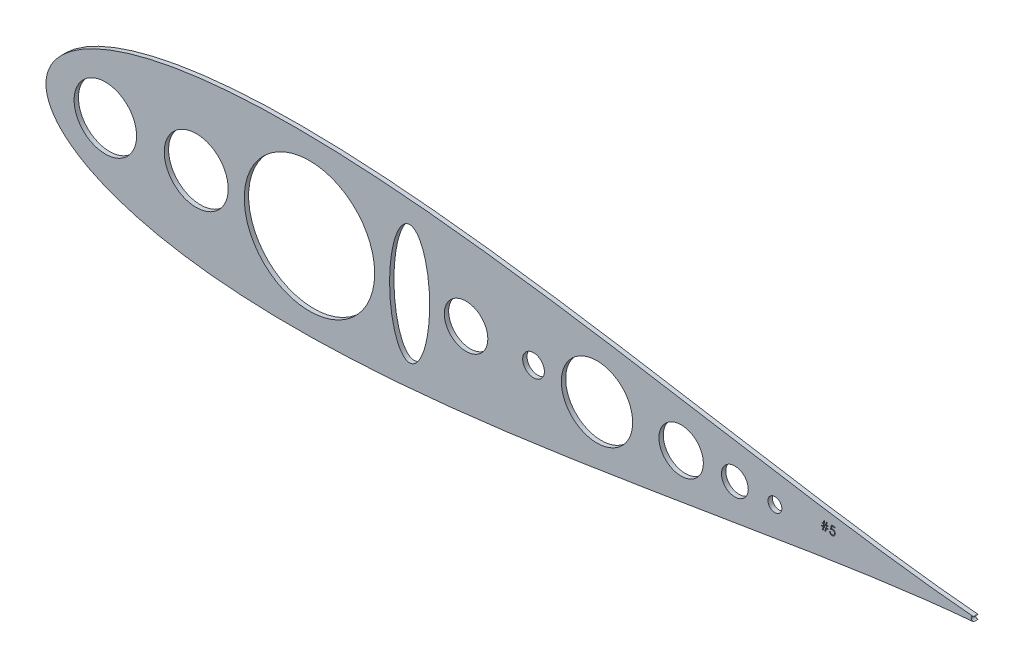
SolidWorks part; units mm, degrees
ref_plane "Front Plane" through (0, 0, 0) normal (0, 0, 1) x (1, 0, 0)
ref_plane "Top Plane" through (0, 0, 0) normal (0, 1, 0) x (1, 0, 0)
ref_plane "Right Plane" through (0, 0, 0) normal (1, 0, 0) x (0, 0, -1)
sketch "Model" plane through (0, 0, 0) normal (0, 0, 1) x (1, 0, 0)
  line L0 (738.2935, 524.3398) -> (738.2935, 524.0142)
  line L1 (738.2935, 524.0142) -> (737.3226, 524.0142)
  line L2 (737.3226, 524.0142) -> (737.0591, 522.2557)
  line L3 (737.0591, 522.2557) -> (736.6653, 522.2557)
  line L4 (736.6653, 522.2557) -> (736.9288, 524.0142)
  line L5 (736.9288, 524.0142) -> (735.8898, 524.0142)
  line L6 (735.8898, 524.0142) -> (735.6263, 522.2557)
  line L7 (735.6263, 522.2557) -> (735.2324, 522.2557)
  line L8 (735.2324, 522.2557) -> (735.496, 524.0142)
  line L9 (735.496, 524.0142) -> (734.6463, 524.0142)
  line L10 (734.6463, 524.0142) -> (734.6463, 524.3398)
  line L11 (734.6463, 524.3398) -> (735.5449, 524.3398)
  line L12 (735.5449, 524.3398) -> (735.7209, 525.5121)
  line L13 (735.7209, 525.5121) -> (734.7765, 525.5121)
  line L14 (734.7765, 525.5121) -> (734.7765, 525.8378)
  line L15 (734.7765, 525.8378) -> (735.7697, 525.8378)
  line L16 (735.7697, 525.8378) -> (736.014, 527.466)
  line L17 (736.014, 527.466) -> (736.4068, 527.466)
  line L18 (736.4068, 527.466) -> (736.1626, 525.8378)
  line L19 (736.1626, 525.8378) -> (737.2026, 525.8378)
  line L20 (737.2026, 525.8378) -> (737.4468, 527.466)
  line L21 (737.4468, 527.466) -> (737.8396, 527.466)
  line L22 (737.8396, 527.466) -> (737.5954, 525.8378)
  line L23 (737.5954, 525.8378) -> (738.4237, 525.8378)
  line L24 (738.4237, 525.8378) -> (738.4237, 525.5121)
  line L25 (738.4237, 525.5121) -> (737.5465, 525.5121)
  line L26 (737.5465, 525.5121) -> (737.3715, 524.3398)
  line L27 (737.3715, 524.3398) -> (738.2935, 524.3398)
  line L28 (737.1537, 525.5121) -> (736.1137, 525.5121)
  line L29 (736.1137, 525.5121) -> (735.9387, 524.3398)
  line L30 (735.9387, 524.3398) -> (736.9777, 524.3398)
  line L31 (736.9777, 524.3398) -> (737.1537, 525.5121)
  line L32 (742.4617, 527.3357) -> (742.4617, 526.8147)
  line L33 (742.4617, 526.8147) -> (740.7337, 526.8147)
  line L34 (740.7337, 526.8147) -> (740.46, 525.4786)
  line L35 (740.46, 525.4786) -> (740.6218, 525.5213)
  line L36 (740.6218, 525.5213) -> (740.7755, 525.5528)
  line L37 (740.7755, 525.5528) -> (740.921, 525.5712)
  line L38 (740.921, 525.5712) -> (741.0584, 525.5773)
  line L39 (741.0584, 525.5773) -> (741.2283, 525.5701)
  line L40 (741.2283, 525.5701) -> (741.3911, 525.5478)
  line L41 (741.3911, 525.5478) -> (741.5458, 525.5111)
  line L42 (741.5458, 525.5111) -> (741.6934, 525.4602)
  line L43 (741.6934, 525.4602) -> (741.8328, 525.3951)
  line L44 (741.8328, 525.3951) -> (741.9641, 525.3147)
  line L45 (741.9641, 525.3147) -> (742.0882, 525.2201)
  line L46 (742.0882, 525.2201) -> (742.2052, 525.1102)
  line L47 (742.2052, 525.1102) -> (742.3111, 524.9891)
  line L48 (742.3111, 524.9891) -> (742.4026, 524.8609)
  line L49 (742.4026, 524.8609) -> (742.481, 524.7235)
  line L50 (742.481, 524.7235) -> (742.5441, 524.579)
  line L51 (742.5441, 524.579) -> (742.594, 524.4253)
  line L52 (742.594, 524.4253) -> (742.6286, 524.2635)
  line L53 (742.6286, 524.2635) -> (742.6499, 524.0936)
  line L54 (742.6499, 524.0936) -> (742.6571, 523.9155)
  line L55 (742.6571, 523.9155) -> (742.653, 523.7913)
  line L56 (742.653, 523.7913) -> (742.6428, 523.6692)
  line L57 (742.6428, 523.6692) -> (742.6245, 523.5502)
  line L58 (742.6245, 523.5502) -> (742.5991, 523.4331)
  line L59 (742.5991, 523.4331) -> (742.5665, 523.3192)
  line L60 (742.5665, 523.3192) -> (742.5268, 523.2082)
  line L61 (742.5268, 523.2082) -> (742.479, 523.0993)
  line L62 (742.479, 523.0993) -> (742.425, 522.9925)
  line L63 (742.425, 522.9925) -> (742.365, 522.8907)
  line L64 (742.365, 522.8907) -> (742.2989, 522.7951)
  line L65 (742.2989, 522.7951) -> (742.2286, 522.7055)
  line L66 (742.2286, 522.7055) -> (742.1533, 522.6221)
  line L67 (742.1533, 522.6221) -> (742.0719, 522.5447)
  line L68 (742.0719, 522.5447) -> (741.9854, 522.4735)
  line L69 (741.9854, 522.4735) -> (741.8949, 522.4084)
  line L70 (741.8949, 522.4084) -> (741.7982, 522.3494)
  line L71 (741.7982, 522.3494) -> (741.6974, 522.2964)
  line L72 (741.6974, 522.2964) -> (741.5926, 522.2517)
  line L73 (741.5926, 522.2517) -> (741.4847, 522.213)
  line L74 (741.4847, 522.213) -> (741.3728, 522.1814)
  line L75 (741.3728, 522.1814) -> (741.2568, 522.157)
  line L76 (741.2568, 522.157) -> (741.1367, 522.1397)
  line L77 (741.1367, 522.1397) -> (741.0126, 522.1285)
  line L78 (741.0126, 522.1285) -> (740.8854, 522.1255)
  line L79 (740.8854, 522.1255) -> (740.7337, 522.1316)
  line L80 (740.7337, 522.1316) -> (740.5882, 522.1509)
  line L81 (740.5882, 522.1509) -> (740.4488, 522.1814)
  line L82 (740.4488, 522.1814) -> (740.3155, 522.2252)
  line L83 (740.3155, 522.2252) -> (740.1883, 522.2812)
  line L84 (740.1883, 522.2812) -> (740.0672, 522.3504)
  line L85 (740.0672, 522.3504) -> (739.9512, 522.4308)
  line L86 (739.9512, 522.4308) -> (739.8423, 522.5244)
  line L87 (739.8423, 522.5244) -> (739.7416, 522.6282)
  line L88 (739.7416, 522.6282) -> (739.652, 522.7391)
  line L89 (739.652, 522.7391) -> (739.5726, 522.8572)
  line L90 (739.5726, 522.8572) -> (739.5034, 522.9833)
  line L91 (739.5034, 522.9833) -> (739.4454, 523.1156)
  line L92 (739.4454, 523.1156) -> (739.3986, 523.2561)
  line L93 (739.3986, 523.2561) -> (739.362, 523.4036)
  line L94 (739.362, 523.4036) -> (739.3355, 523.5583)
  line L95 (739.3355, 523.5583) -> (739.7914, 523.5583)
  line L96 (739.7914, 523.5583) -> (739.828, 523.4138)
  line L97 (739.828, 523.4138) -> (739.8749, 523.2846)
  line L98 (739.8749, 523.2846) -> (739.9329, 523.1685)
  line L99 (739.9329, 523.1685) -> (740.001, 523.0668)
  line L100 (740.001, 523.0668) -> (740.0814, 522.9772)
  line L101 (740.0814, 522.9772) -> (740.174, 522.8968)
  line L102 (740.174, 522.8968) -> (740.2789, 522.8246)
  line L103 (740.2789, 522.8246) -> (740.3959, 522.7625)
  line L104 (740.3959, 522.7625) -> (740.52, 522.7116)
  line L105 (740.52, 522.7116) -> (740.6483, 522.676)
  line L106 (740.6483, 522.676) -> (740.7785, 522.6536)
  line L107 (740.7785, 522.6536) -> (740.9118, 522.6465)
  line L108 (740.9118, 522.6465) -> (741.0421, 522.6526)
  line L109 (741.0421, 522.6526) -> (741.1672, 522.6699)
  line L110 (741.1672, 522.6699) -> (741.2883, 522.6984)
  line L111 (741.2883, 522.6984) -> (741.4044, 522.7391)
  line L112 (741.4044, 522.7391) -> (741.5153, 522.79)
  line L113 (741.5153, 522.79) -> (741.6221, 522.8541)
  line L114 (741.6221, 522.8541) -> (741.7239, 522.9284)
  line L115 (741.7239, 522.9284) -> (741.8216, 523.0149)
  line L116 (741.8216, 523.0149) -> (741.9101, 523.1095)
  line L117 (741.9101, 523.1095) -> (741.9875, 523.2103)
  line L118 (741.9875, 523.2103) -> (742.0526, 523.3171)
  line L119 (742.0526, 523.3171) -> (742.1065, 523.4291)
  line L120 (742.1065, 523.4291) -> (742.1482, 523.5471)
  line L121 (742.1482, 523.5471) -> (742.1778, 523.6702)
  line L122 (742.1778, 523.6702) -> (742.1951, 523.7995)
  line L123 (742.1951, 523.7995) -> (742.2012, 523.9348)
  line L124 (742.2012, 523.9348) -> (742.1961, 524.0569)
  line L125 (742.1961, 524.0569) -> (742.1808, 524.1729)
  line L126 (742.1808, 524.1729) -> (742.1543, 524.2828)
  line L127 (742.1543, 524.2828) -> (742.1177, 524.3866)
  line L128 (742.1177, 524.3866) -> (742.0709, 524.4854)
  line L129 (742.0709, 524.4854) -> (742.0139, 524.578)
  line L130 (742.0139, 524.578) -> (741.9457, 524.6645)
  line L131 (741.9457, 524.6645) -> (741.8674, 524.7449)
  line L132 (741.8674, 524.7449) -> (741.7809, 524.8181)
  line L133 (741.7809, 524.8181) -> (741.6862, 524.8812)
  line L134 (741.6862, 524.8812) -> (741.5855, 524.9341)
  line L135 (741.5855, 524.9341) -> (741.4776, 524.9789)
  line L136 (741.4776, 524.9789) -> (741.3626, 525.0125)
  line L137 (741.3626, 525.0125) -> (741.2405, 525.0369)
  line L138 (741.2405, 525.0369) -> (741.1123, 525.0512)
  line L139 (741.1123, 525.0512) -> (740.9759, 525.0562)
  line L140 (740.9759, 525.0562) -> (740.8579, 525.0522)
  line L141 (740.8579, 525.0522) -> (740.7327, 525.04)
  line L142 (740.7327, 525.04) -> (740.6025, 525.0196)
  line L143 (740.6025, 525.0196) -> (740.4651, 524.9911)
  line L144 (740.4651, 524.9911) -> (740.3226, 524.9545)
  line L145 (740.3226, 524.9545) -> (740.173, 524.9097)
  line L146 (740.173, 524.9097) -> (740.0183, 524.8568)
  line L147 (740.0183, 524.8568) -> (739.8565, 524.7957)
  line L148 (739.8565, 524.7957) -> (740.3776, 527.3357)
  line L149 (740.3776, 527.3357) -> (742.4617, 527.3357)
  circle A0 centre (316.6495, 521.1085) radius 18.2309
  circle A1 centre (707.4198, 521.1085) radius 4.0377
  circle A2 centre (684.0578, 521.1085) radius 7.8218
  circle A3 centre (652.7021, 521.1085) radius 12.9578
  circle A4 centre (603.5976, 521.1085) radius 20.8135
  circle A5 centre (566.5539, 521.1085) radius 6.35
  circle A6 centre (527.1839, 521.1085) radius 12.7
  circle A7 centre (435.7938, 521.1085) radius 38.053
  circle A8 centre (369.7039, 521.1085) radius 18.669
  arc A9 (823.4212, 522.34) -> (823.4192, 519.8762) centre (823.2427, 521.1082) ccw
  arc A10 (823.4212, 522.34) -> (823.0121, 522.4406) centre (822.9014, 521.1085) ccw
  arc A11 (823.0121, 519.7764) -> (823.4192, 519.8762) centre (822.9014, 521.1085) ccw
  ellipse E0 centre (494.2426, 521.1085) end of major axis (494.2426, 486.1605) minor radius 11.7082
  spline S0 degree 3 poles (823.0121, 522.4406) (822.5764, 522.4768) (819.2929, 522.7534) (812.8264, 523.3511) (803.2279, 524.3496) (792.5858, 525.5748) (780.94, 527.0342) (768.345, 528.7291) (754.8551, 530.6559) (740.5289, 532.8045) (725.4271, 535.1596) (709.6131, 537.7002) (693.1521, 540.4001) (676.1114, 543.2282) (658.5599, 546.1488) (640.5682, 549.1221) (622.2082, 552.1052) (603.5531, 555.0523) (584.6777, 557.9153) (565.658, 560.645) (546.5712, 563.1915) (527.4962, 565.5052) (508.5129, 567.5374) (489.7028, 569.2411) (471.1488, 570.572) (452.9349, 571.4888) (435.1468, 571.9548) (417.8712, 571.9375) (401.1964, 571.4095) (385.2119, 570.3502) (370.009, 568.7441) (355.6804, 566.584) (342.3218, 563.8693) (330.032, 560.6089) (318.9148, 556.8219) (309.0813, 552.5422) (300.6507, 547.8264) (293.7491, 542.7702) (288.4927, 537.5386) (284.934, 532.4085) (282.9495, 527.78) (282.1482, 524.0671) (281.9657, 521.1085) (282.1482, 518.1499) (282.9495, 514.437) (284.934, 509.8086) (288.4927, 504.6784) (293.7491, 499.4469) (300.6507, 494.3906) (309.0813, 489.6748) (318.9148, 485.3951) (330.032, 481.6082) (342.3218, 478.3478) (355.6804, 475.633) (370.009, 473.4729) (385.2119, 471.8669) (401.1964, 470.8075) (417.8712, 470.2795) (435.1468, 470.2622) (452.9349, 470.7282) (471.1488, 471.6451) (489.7028, 472.9759) (508.5129, 474.6796) (527.4962, 476.7118) (546.5712, 479.0255) (565.658, 481.572) (584.6777, 484.3017) (603.5531, 487.1647) (622.2082, 490.1118) (640.5682, 493.0949) (658.5599, 496.0683) (676.1114, 498.9888) (693.1521, 501.8169) (709.6131, 504.5168) (725.4271, 507.0575) (740.5289, 509.4126) (754.8551, 511.5611) (768.345, 513.4879) (780.94, 515.1828) (792.5858, 516.6422) (803.2279, 517.8674) (812.8264, 518.8659) (819.2929, 519.4636) (822.5764, 519.7402) (823.0121, 519.7764) knots 0.020157 0.020157 0.020157 0.020157 0.021271 0.028553 0.036781 0.04592 0.055932 0.066773 0.078397 0.090755 0.103793 0.117456 0.131686 0.146422 0.1616 0.177156 0.193024 0.209135 0.225421 0.241812 0.258238 0.274629 0.290914 0.307025 0.322893 0.338448 0.353626 0.368361 0.38259 0.396253 0.40929 0.421647 0.43327 0.444109 0.454119 0.463255 0.471479 0.478755 0.485052 0.490344 0.49461 0.497833 0.5 0.502167 0.50539 0.509656 0.514948 0.521245 0.528521 0.536745 0.545881 0.555891 0.56673 0.578353 0.59071 0.603747 0.61741 0.631639 0.646374 0.661552 0.677107 0.692975 0.709086 0.725371 0.741762 0.758188 0.774579 0.790865 0.806976 0.822844 0.8384 0.853578 0.868314 0.882544 0.896207 0.909245 0.921603 0.933227 0.944068 0.95408 0.963219 0.971447 0.978729 0.979843 0.979843 0.979843 0.979843
sketch "Sketch2" plane through (0, 0, 0) normal (0, 0, 1) x (1, 0, 0)
  line L0 (738.2935, 524.3398) -> (738.2935, 524.0142)
  line L1 (738.2935, 524.0142) -> (737.3226, 524.0142)
  line L2 (737.3226, 524.0142) -> (737.0591, 522.2557)
  line L3 (737.0591, 522.2557) -> (736.6653, 522.2557)
  line L4 (736.6653, 522.2557) -> (736.9288, 524.0142)
  line L5 (736.9288, 524.0142) -> (735.8898, 524.0142)
  line L6 (735.8898, 524.0142) -> (735.6263, 522.2557)
  line L7 (735.6263, 522.2557) -> (735.2324, 522.2557)
  line L8 (735.2324, 522.2557) -> (735.496, 524.0142)
  line L9 (735.496, 524.0142) -> (734.6463, 524.0142)
  line L10 (734.6463, 524.0142) -> (734.6463, 524.3398)
  line L11 (734.6463, 524.3398) -> (735.5449, 524.3398)
  line L12 (735.5449, 524.3398) -> (735.7209, 525.5121)
  line L13 (735.7209, 525.5121) -> (734.7765, 525.5121)
  line L14 (734.7765, 525.5121) -> (734.7765, 525.8378)
  line L15 (734.7765, 525.8378) -> (735.7697, 525.8378)
  line L16 (735.7697, 525.8378) -> (736.014, 527.466)
  line L17 (736.014, 527.466) -> (736.4068, 527.466)
  line L18 (736.4068, 527.466) -> (736.1626, 525.8378)
  line L19 (736.1626, 525.8378) -> (737.2026, 525.8378)
  line L20 (737.2026, 525.8378) -> (737.4468, 527.466)
  line L21 (737.4468, 527.466) -> (737.8396, 527.466)
  line L22 (737.8396, 527.466) -> (737.5954, 525.8378)
  line L23 (737.5954, 525.8378) -> (738.4237, 525.8378)
  line L24 (738.4237, 525.8378) -> (738.4237, 525.5121)
  line L25 (738.4237, 525.5121) -> (737.5465, 525.5121)
  line L26 (737.5465, 525.5121) -> (737.3715, 524.3398)
  line L27 (737.3715, 524.3398) -> (738.2935, 524.3398)
  line L28 (737.1537, 525.5121) -> (736.1137, 525.5121)
  line L29 (736.1137, 525.5121) -> (735.9387, 524.3398)
  line L30 (735.9387, 524.3398) -> (736.9777, 524.3398)
  line L31 (736.9777, 524.3398) -> (737.1537, 525.5121)
  line L32 (742.4617, 527.3357) -> (742.4617, 526.8147)
  line L33 (742.4617, 526.8147) -> (740.7337, 526.8147)
  line L34 (740.7337, 526.8147) -> (740.46, 525.4786)
  line L35 (740.46, 525.4786) -> (740.6218, 525.5213)
  line L36 (740.6218, 525.5213) -> (740.7755, 525.5528)
  line L37 (740.7755, 525.5528) -> (740.921, 525.5712)
  line L38 (740.921, 525.5712) -> (741.0584, 525.5773)
  line L39 (741.0584, 525.5773) -> (741.2283, 525.5701)
  line L40 (741.2283, 525.5701) -> (741.3911, 525.5478)
  line L41 (741.3911, 525.5478) -> (741.5458, 525.5111)
  line L42 (741.5458, 525.5111) -> (741.6934, 525.4602)
  line L43 (741.6934, 525.4602) -> (741.8328, 525.3951)
  line L44 (741.8328, 525.3951) -> (741.9641, 525.3147)
  line L45 (741.9641, 525.3147) -> (742.0882, 525.2201)
  line L46 (742.0882, 525.2201) -> (742.2052, 525.1102)
  line L47 (742.2052, 525.1102) -> (742.3111, 524.9891)
  line L48 (742.3111, 524.9891) -> (742.4026, 524.8609)
  line L49 (742.4026, 524.8609) -> (742.481, 524.7235)
  line L50 (742.481, 524.7235) -> (742.5441, 524.579)
  line L51 (742.5441, 524.579) -> (742.594, 524.4253)
  line L52 (742.594, 524.4253) -> (742.6286, 524.2635)
  line L53 (742.6286, 524.2635) -> (742.6499, 524.0936)
  line L54 (742.6499, 524.0936) -> (742.6571, 523.9155)
  line L55 (742.6571, 523.9155) -> (742.653, 523.7913)
  line L56 (742.653, 523.7913) -> (742.6428, 523.6692)
  line L57 (742.6428, 523.6692) -> (742.6245, 523.5502)
  line L58 (742.6245, 523.5502) -> (742.5991, 523.4331)
  line L59 (742.5991, 523.4331) -> (742.5665, 523.3192)
  line L60 (742.5665, 523.3192) -> (742.5268, 523.2082)
  line L61 (742.5268, 523.2082) -> (742.479, 523.0993)
  line L62 (742.479, 523.0993) -> (742.425, 522.9925)
  line L63 (742.425, 522.9925) -> (742.365, 522.8907)
  line L64 (742.365, 522.8907) -> (742.2989, 522.7951)
  line L65 (742.2989, 522.7951) -> (742.2286, 522.7055)
  line L66 (742.2286, 522.7055) -> (742.1533, 522.6221)
  line L67 (742.1533, 522.6221) -> (742.0719, 522.5447)
  line L68 (742.0719, 522.5447) -> (741.9854, 522.4735)
  line L69 (741.9854, 522.4735) -> (741.8949, 522.4084)
  line L70 (741.8949, 522.4084) -> (741.7982, 522.3494)
  line L71 (741.7982, 522.3494) -> (741.6974, 522.2964)
  line L72 (741.6974, 522.2964) -> (741.5926, 522.2517)
  line L73 (741.5926, 522.2517) -> (741.4847, 522.213)
  line L74 (741.4847, 522.213) -> (741.3728, 522.1814)
  line L75 (741.3728, 522.1814) -> (741.2568, 522.157)
  line L76 (741.2568, 522.157) -> (741.1367, 522.1397)
  line L77 (741.1367, 522.1397) -> (741.0126, 522.1285)
  line L78 (741.0126, 522.1285) -> (740.8854, 522.1255)
  line L79 (740.8854, 522.1255) -> (740.7337, 522.1316)
  line L80 (740.7337, 522.1316) -> (740.5882, 522.1509)
  line L81 (740.5882, 522.1509) -> (740.4488, 522.1814)
  line L82 (740.4488, 522.1814) -> (740.3155, 522.2252)
  line L83 (740.3155, 522.2252) -> (740.1883, 522.2812)
  line L84 (740.1883, 522.2812) -> (740.0672, 522.3504)
  line L85 (740.0672, 522.3504) -> (739.9512, 522.4308)
  line L86 (739.9512, 522.4308) -> (739.8423, 522.5244)
  line L87 (739.8423, 522.5244) -> (739.7416, 522.6282)
  line L88 (739.7416, 522.6282) -> (739.652, 522.7391)
  line L89 (739.652, 522.7391) -> (739.5726, 522.8572)
  line L90 (739.5726, 522.8572) -> (739.5034, 522.9833)
  line L91 (739.5034, 522.9833) -> (739.4454, 523.1156)
  line L92 (739.4454, 523.1156) -> (739.3986, 523.2561)
  line L93 (739.3986, 523.2561) -> (739.362, 523.4036)
  line L94 (739.362, 523.4036) -> (739.3355, 523.5583)
  line L95 (739.3355, 523.5583) -> (739.7914, 523.5583)
  line L96 (739.7914, 523.5583) -> (739.828, 523.4138)
  line L97 (739.828, 523.4138) -> (739.8749, 523.2846)
  line L98 (739.8749, 523.2846) -> (739.9329, 523.1685)
  line L99 (739.9329, 523.1685) -> (740.001, 523.0668)
  line L100 (740.001, 523.0668) -> (740.0814, 522.9772)
  line L101 (740.0814, 522.9772) -> (740.174, 522.8968)
  line L102 (740.174, 522.8968) -> (740.2789, 522.8246)
  line L103 (740.2789, 522.8246) -> (740.3959, 522.7625)
  line L104 (740.3959, 522.7625) -> (740.52, 522.7116)
  line L105 (740.52, 522.7116) -> (740.6483, 522.676)
  line L106 (740.6483, 522.676) -> (740.7785, 522.6536)
  line L107 (740.7785, 522.6536) -> (740.9118, 522.6465)
  line L108 (740.9118, 522.6465) -> (741.0421, 522.6526)
  line L109 (741.0421, 522.6526) -> (741.1672, 522.6699)
  line L110 (741.1672, 522.6699) -> (741.2883, 522.6984)
  line L111 (741.2883, 522.6984) -> (741.4044, 522.7391)
  line L112 (741.4044, 522.7391) -> (741.5153, 522.79)
  line L113 (741.5153, 522.79) -> (741.6221, 522.8541)
  line L114 (741.6221, 522.8541) -> (741.7239, 522.9284)
  line L115 (741.7239, 522.9284) -> (741.8216, 523.0149)
  line L116 (741.8216, 523.0149) -> (741.9101, 523.1095)
  line L117 (741.9101, 523.1095) -> (741.9875, 523.2103)
  line L118 (741.9875, 523.2103) -> (742.0526, 523.3171)
  line L119 (742.0526, 523.3171) -> (742.1065, 523.4291)
  line L120 (742.1065, 523.4291) -> (742.1482, 523.5471)
  line L121 (742.1482, 523.5471) -> (742.1778, 523.6702)
  line L122 (742.1778, 523.6702) -> (742.1951, 523.7995)
  line L123 (742.1951, 523.7995) -> (742.2012, 523.9348)
  line L124 (742.2012, 523.9348) -> (742.1961, 524.0569)
  line L125 (742.1961, 524.0569) -> (742.1808, 524.1729)
  line L126 (742.1808, 524.1729) -> (742.1543, 524.2828)
  line L127 (742.1543, 524.2828) -> (742.1177, 524.3866)
  line L128 (742.1177, 524.3866) -> (742.0709, 524.4854)
  line L129 (742.0709, 524.4854) -> (742.0139, 524.578)
  line L130 (742.0139, 524.578) -> (741.9457, 524.6645)
  line L131 (741.9457, 524.6645) -> (741.8674, 524.7449)
  line L132 (741.8674, 524.7449) -> (741.7809, 524.8181)
  line L133 (741.7809, 524.8181) -> (741.6862, 524.8812)
  line L134 (741.6862, 524.8812) -> (741.5855, 524.9341)
  line L135 (741.5855, 524.9341) -> (741.4776, 524.9789)
  line L136 (741.4776, 524.9789) -> (741.3626, 525.0125)
  line L137 (741.3626, 525.0125) -> (741.2405, 525.0369)
  line L138 (741.2405, 525.0369) -> (741.1123, 525.0512)
  line L139 (741.1123, 525.0512) -> (740.9759, 525.0562)
  line L140 (740.9759, 525.0562) -> (740.8579, 525.0522)
  line L141 (740.8579, 525.0522) -> (740.7327, 525.04)
  line L142 (740.7327, 525.04) -> (740.6025, 525.0196)
  line L143 (740.6025, 525.0196) -> (740.4651, 524.9911)
  line L144 (740.4651, 524.9911) -> (740.3226, 524.9545)
  line L145 (740.3226, 524.9545) -> (740.173, 524.9097)
  line L146 (740.173, 524.9097) -> (740.0183, 524.8568)
  line L147 (740.0183, 524.8568) -> (739.8565, 524.7957)
  line L148 (739.8565, 524.7957) -> (740.3776, 527.3357)
  line L149 (740.3776, 527.3357) -> (742.4617, 527.3357)
  circle A0 centre (316.6495, 521.1085) radius 18.2309
  circle A1 centre (707.4198, 521.1085) radius 4.0377
  circle A2 centre (684.0578, 521.1085) radius 7.8218
  circle A3 centre (652.7021, 521.1085) radius 12.9578
  circle A4 centre (603.5976, 521.1085) radius 20.8135
  circle A5 centre (566.5539, 521.1085) radius 6.35
  circle A6 centre (527.1839, 521.1085) radius 12.7
  circle A7 centre (435.7938, 521.1085) radius 38.053
  circle A8 centre (369.7039, 521.1085) radius 18.669
  arc A9 (823.4212, 522.34) -> (823.4192, 519.8762) centre (823.2427, 521.1082) ccw
  arc A10 (823.4212, 522.34) -> (823.0121, 522.4406) centre (822.9014, 521.1085) ccw
  arc A11 (823.0121, 519.7764) -> (823.4192, 519.8762) centre (822.9014, 521.1085) ccw
  ellipse E0 centre (494.2426, 521.1085) end of major axis (494.2426, 486.1605) minor radius 11.7082
  spline S0 degree 3 poles (823.0121, 522.4406) (822.5764, 522.4768) (819.2929, 522.7534) (812.8264, 523.3511) (803.2279, 524.3496) (792.5858, 525.5748) (780.94, 527.0342) (768.345, 528.7291) (754.8551, 530.6559) (740.5289, 532.8045) (725.4271, 535.1596) (709.6131, 537.7002) (693.1521, 540.4001) (676.1114, 543.2282) (658.5599, 546.1488) (640.5682, 549.1221) (622.2082, 552.1052) (603.5531, 555.0523) (584.6777, 557.9153) (565.658, 560.645) (546.5712, 563.1915) (527.4962, 565.5052) (508.5129, 567.5374) (489.7028, 569.2411) (471.1488, 570.572) (452.9349, 571.4888) (435.1468, 571.9548) (417.8712, 571.9375) (401.1964, 571.4095) (385.2119, 570.3502) (370.009, 568.7441) (355.6804, 566.584) (342.3218, 563.8693) (330.032, 560.6089) (318.9148, 556.8219) (309.0813, 552.5422) (300.6507, 547.8264) (293.7491, 542.7702) (288.4927, 537.5386) (284.934, 532.4085) (282.9495, 527.78) (282.1482, 524.0671) (281.9657, 521.1085) (282.1482, 518.1499) (282.9495, 514.437) (284.934, 509.8086) (288.4927, 504.6784) (293.7491, 499.4469) (300.6507, 494.3906) (309.0813, 489.6748) (318.9148, 485.3951) (330.032, 481.6082) (342.3218, 478.3478) (355.6804, 475.633) (370.009, 473.4729) (385.2119, 471.8669) (401.1964, 470.8075) (417.8712, 470.2795) (435.1468, 470.2622) (452.9349, 470.7282) (471.1488, 471.6451) (489.7028, 472.9759) (508.5129, 474.6796) (527.4962, 476.7118) (546.5712, 479.0255) (565.658, 481.572) (584.6777, 484.3017) (603.5531, 487.1647) (622.2082, 490.1118) (640.5682, 493.0949) (658.5599, 496.0683) (676.1114, 498.9888) (693.1521, 501.8169) (709.6131, 504.5168) (725.4271, 507.0575) (740.5289, 509.4126) (754.8551, 511.5611) (768.345, 513.4879) (780.94, 515.1828) (792.5858, 516.6422) (803.2279, 517.8674) (812.8264, 518.8659) (819.2929, 519.4636) (822.5764, 519.7402) (823.0121, 519.7764) knots 0.020157 0.020157 0.020157 0.020157 0.021271 0.028553 0.036781 0.04592 0.055932 0.066773 0.078397 0.090755 0.103793 0.117456 0.131686 0.146422 0.1616 0.177156 0.193024 0.209135 0.225421 0.241812 0.258238 0.274629 0.290914 0.307025 0.322893 0.338448 0.353626 0.368361 0.38259 0.396253 0.40929 0.421647 0.43327 0.444109 0.454119 0.463255 0.471479 0.478755 0.485052 0.490344 0.49461 0.497833 0.5 0.502167 0.50539 0.509656 0.514948 0.521245 0.528521 0.536745 0.545881 0.555891 0.56673 0.578353 0.59071 0.603747 0.61741 0.631639 0.646374 0.661552 0.677107 0.692975 0.709086 0.725371 0.741762 0.758188 0.774579 0.790865 0.806976 0.822844 0.8384 0.853578 0.868314 0.882544 0.896207 0.909245 0.921603 0.933227 0.944068 0.95408 0.963219 0.971447 0.978729 0.979843 0.979843 0.979843 0.979843
extrude "Boss-Extrude1" add sketch "Sketch2" along normal blind 2.54 contours A10 S0 A11 A9 L148 L149 L32 L33 L34 L35 L36 L37 L38 L39 L40 L41 L42 L43 L44 L45 L46 L47 L48 L49 L50 L51 L52 L53 L54 L55 L56 L57 L58 L59 L60 L61 L62 L63 L64 L65 L66 L67 L68 L69 L70 L71 L72 L73 L74 L75
